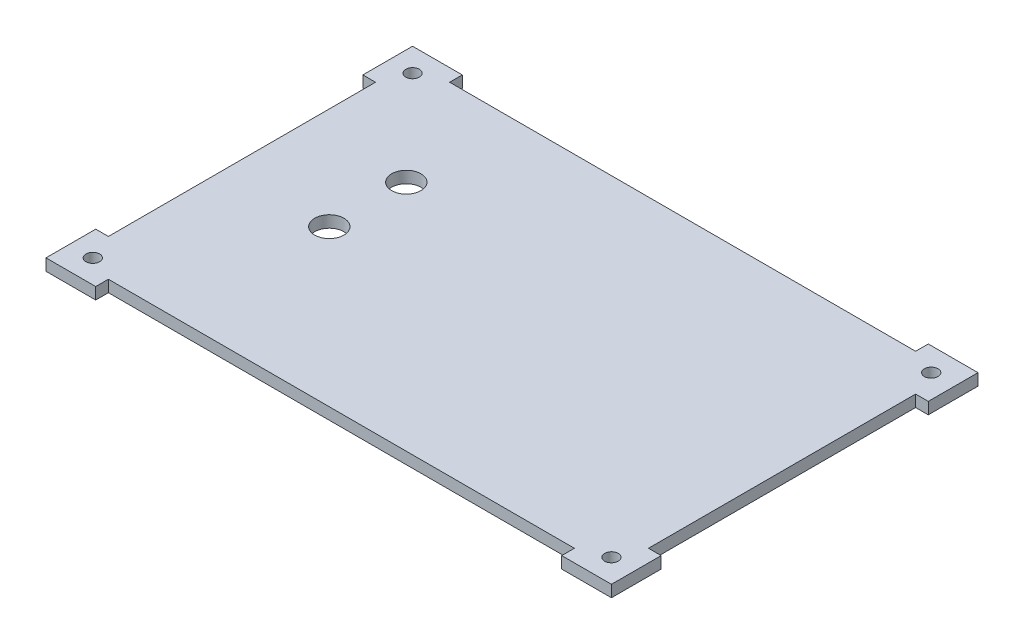
SolidWorks part; units mm, degrees
ref_plane "Front Plane" through (0, 0, 0) normal (0, 0, 1) x (1, 0, 0)
ref_plane "Top Plane" through (0, 0, 0) normal (0, 1, 0) x (1, 0, 0)
ref_plane "Right Plane" through (0, 0, 0) normal (1, 0, 0) x (0, 0, -1)
sketch "Sketch1" plane through (0, 0, 0) normal (0, 1, 0) x (1, 0, 0)
  line L1 (0, 0) -> (138.5, 0)
  line L2 (0, 0) -> (0, -87.5)
  line L3 (0, -87.5) -> (138.5, -87.5)
  line L4 (138.5, 0) -> (138.5, -87.5)
  dimension "D1" = 138.5
  dimension "D2" = 87.5
extrude "Boss-Extrude1" add sketch "Sketch1" along normal blind 3
sketch "Sketch2" plane through (0, 0, 0) normal (0, -1, 0) x (1, 0, 0)
  line L0 (0, 0) -> (0, 87.5) construction
  line L1 (0, 87.5) -> (138.5, 87.5) construction
  line L2 (138.5, 0) -> (0, 0) construction
  line L3 (138.5, 87.5) -> (138.5, 0) construction
  circle A0 centre (2.75, 84.75) radius 1.75
  circle A1 centre (135.75, 84.75) radius 1.75
  circle A2 centre (135.75, 2.75) radius 1.75
  circle A3 centre (2.75, 2.75) radius 1.75
  dimension "D1" = 3.5
  dimension "D2" = 2.75
  dimension "D3" = 2.75
  dimension "D4" = 2.75
  dimension "D5" = 2.75
  dimension "D6" = 2.75
  dimension "D7" = 2.75
  dimension "D8" = 2.75
  dimension "D9" = 2.75
extrude "Cut-Extrude1" cut sketch "Sketch2" against normal through all
sketch "Sketch3" plane through (0, 0, 0) normal (0, -1, 0) x (1, 0, 0)
  line L0 (0, 0) -> (0, 87.5) construction
  line L1 (-3.25, 90.75) -> (0, 90.75)
  line L2 (-3.25, 90.75) -> (-3.25, 78)
  line L3 (-3.25, 78) -> (0, 78)
  line L4 (0, 90.75) -> (0, 78)
  line L5 (0, 87.5) -> (138.5, 87.5) construction
  line L6 (0, 90.75) -> (9.5, 90.75)
  line L7 (0, 90.75) -> (0, 87.5)
  line L8 (0, 87.5) -> (9.5, 87.5)
  line L9 (9.5, 90.75) -> (9.5, 87.5)
  line L10 (138.5, 87.5) -> (138.5, 0) construction
  line L11 (138.5, 87.5) -> (129, 87.5)
  line L12 (138.5, 87.5) -> (138.5, 90.75)
  line L13 (138.5, 90.75) -> (129, 90.75)
  line L14 (129, 87.5) -> (129, 90.75)
  line L15 (138.5, 90.75) -> (141.75, 90.75)
  line L16 (138.5, 90.75) -> (138.5, 78)
  line L17 (138.5, 78) -> (141.75, 78)
  line L18 (141.75, 90.75) -> (141.75, 78)
  line L19 (138.5, 0) -> (0, 0) construction
  line L20 (0, 0) -> (-3.25, 0)
  line L21 (0, 0) -> (0, 9.5)
  line L22 (0, 9.5) -> (-3.25, 9.5)
  line L23 (-3.25, 0) -> (-3.25, 9.5)
  line L24 (-3.25, 0) -> (9.5, 0)
  line L25 (-3.25, 0) -> (-3.25, -3.25)
  line L26 (-3.25, -3.25) -> (9.5, -3.25)
  line L27 (9.5, 0) -> (9.5, -3.25)
  line L29 (138.5, 0) -> (141.75, 0)
  line L30 (138.5, 0) -> (138.5, 9.5)
  line L31 (138.5, 9.5) -> (141.75, 9.5)
  line L32 (141.75, 0) -> (141.75, 9.5)
  line L33 (141.75, 0) -> (129, 0)
  line L34 (141.75, 0) -> (141.75, -3.25)
  line L35 (141.75, -3.25) -> (129, -3.25)
  line L36 (129, 0) -> (129, -3.25)
  line M11 (0, 87.5) -> (0, 0)
  line M12 (0, 0) -> (138.5, 0)
  line M13 (138.5, 0) -> (138.5, 87.5)
  line M14 (138.5, 87.5) -> (0, 87.5)
  dimension "D1" = 9.5
  dimension "D2" = 9.5
  dimension "D3" = 3.25
  dimension "D4" = 3.25
  dimension "D5" = 3.25
  dimension "D6" = 3.25
  dimension "D7" = 9.5
  dimension "D8" = 9.5
  dimension "D9" = 3.25
  dimension "D10" = 3.25
  dimension "D11" = 9.5
  dimension "D12" = 9.5
  dimension "D13" = 3.25
  dimension "D14" = 3.25
  dimension "D15" = 9.5
  dimension "D16" = 9.5
extrude "Boss-Extrude2" add sketch "Sketch3" against normal through all contours L4 L1 L2 L3 M11 | L9 L6 L4 M14 | L23 L20 L22 M11 | L27 L20 L25 L26 M12 | L36 L35 L34 L29 M12 | L29 L32 L31 M13 | L14 L12 L13 M14 | L18 L15 L12 L17 M13
sketch "Sketch4" plane through (0, 0, 0) normal (0, -1, 0) x (1, 0, 0)
  line L0 (0, 9.5) -> (0, 78) construction
  line L1 (9.5, 87.5) -> (129, 87.5) construction
  circle A0 centre (26.15, 47.5) radius 3.75
  circle A1 centre (26.15, 27.75) radius 3.75
  dimension "D1" = 7.5
  dimension "D2" = 7.5
  dimension "D3" = 26.15
  dimension "D4" = 40
  dimension "D5" = 26.15
  dimension "D6" = 19.75
extrude "Cut-Extrude2" cut sketch "Sketch4" against normal through all
equation "\"D4@Sketch2\"=\"D2@Sketch2\""
equation "\"D5@Sketch2\"=\"D4@Sketch2\""
equation "\"D6@Sketch2\"=\"D5@Sketch2\""
equation "\"D7@Sketch2\"=\"D6@Sketch2\""
equation "\"D8@Sketch2\"=\"D2@Sketch2\""
equation "\"D9@Sketch2\"=\"D8@Sketch2\""
equation "\"D2@Sketch4\"=\"D1@Sketch4\""
equation "\"D5@Sketch4\"=\"D3@Sketch4\""
